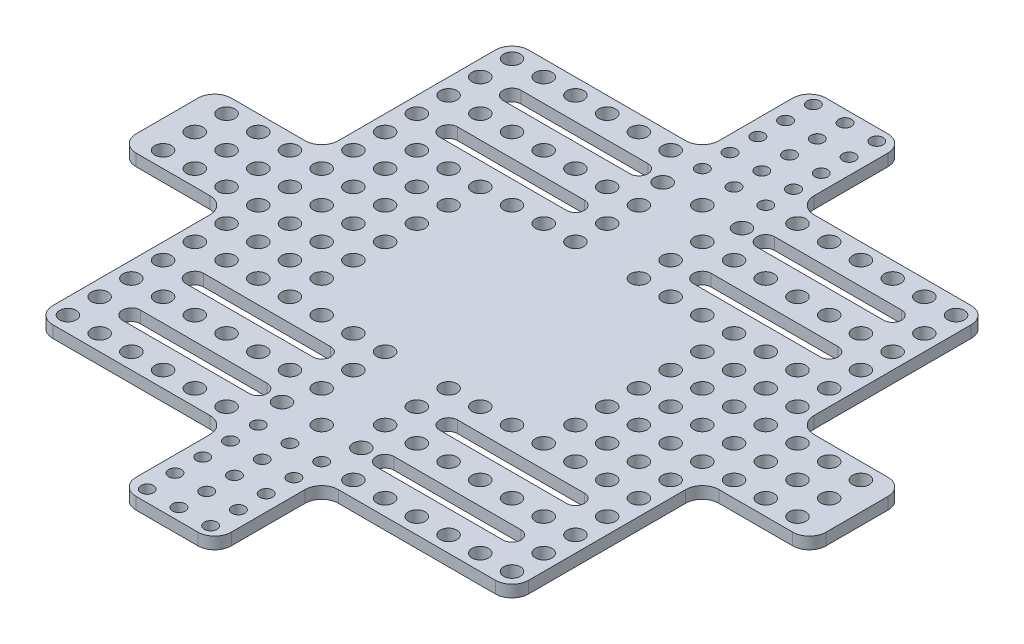
SolidWorks part; units mm, degrees
ref_plane "前视基准面" through (0, 0, 0) normal (0, 0, 1) x (1, 0, 0)
ref_plane "上视基准面" through (0, 0, 0) normal (0, 1, 0) x (1, 0, 0)
ref_plane "右视基准面" through (0, 0, 0) normal (1, 0, 0) x (0, 0, -1)
sketch "草图1" plane through (0, 0, 0) normal (0, 1, 0) x (1, 0, 0)
  line L0 (87, -12) -> (60, -12)
  line L1 (-60, 60) -> (-12, 60)
  line L2 (-60, 60) -> (-60, 12)
  line L3 (-60, -60) -> (-12, -60)
  line L4 (60, 60) -> (60, 12)
  line L5 (-60, 60) -> (60, -60) construction
  line L6 (-60, -60) -> (60, 60) construction
  line L7 (-12, 87) -> (12, 87)
  line L8 (-12, 87) -> (-12, 60)
  line L10 (12, 87) -> (12, 60)
  line L11 (87, 12) -> (60, 12)
  line L12 (87, -12) -> (87, 12)
  line L13 (-87, -12) -> (-60, -12)
  line L14 (-87, 12) -> (-60, 12)
  line L15 (-87, 12) -> (-87, -12)
  line L16 (12, -87) -> (-12, -87)
  line L17 (-12, -87) -> (-12, -60)
  line L18 (12, -87) -> (12, -60)
  line L19 (12, 60) -> (60, 60)
  line L20 (60, -12) -> (60, -60)
  line L21 (-60, -12) -> (-60, -60)
  line L22 (12, -60) -> (60, -60)
  line L23 (-56, 56) -> (-48, 56) construction
  line L24 (0, -20.5615) -> (0, 20.5615) construction
  line L25 (0, 56) -> (0, 63) construction
  line L26 (-56, 16) -> (-48, 16) construction
  line L27 (-56, 16) -> (-56, 8) construction
  line L28 (56, 16) -> (56, 8) construction
  line L29 (56, 16) -> (48, 16) construction
  line L30 (-48, 48) -> (-16, 48) construction
  line L31 (-48, 50.25) -> (-16, 50.25)
  line L32 (-48, 45.75) -> (-16, 45.75)
  line L33 (-56, 40) -> (-48, 40) construction
  line L34 (-48, 32) -> (-16, 32) construction
  line L35 (-48, 34.25) -> (-16, 34.25)
  line L36 (-48, 29.75) -> (-16, 29.75)
  line L37 (-48, 48) -> (-48, 32) construction
  line L38 (48, 32) -> (16, 32) construction
  line L39 (48, 34.25) -> (16, 34.25)
  line L40 (48, 29.75) -> (16, 29.75)
  line L41 (48, 48) -> (16, 48) construction
  line L42 (48, 50.25) -> (16, 50.25)
  line L43 (48, 45.75) -> (16, 45.75)
  line L44 (-55, 0) -> (55, 0) construction
  line L45 (-48, -48) -> (-16, -48) construction
  line L46 (-48, -50.25) -> (-16, -50.25)
  line L47 (-48, -45.75) -> (-16, -45.75)
  line L48 (48, -48) -> (16, -48) construction
  line L49 (48, -50.25) -> (16, -50.25)
  line L50 (48, -45.75) -> (16, -45.75)
  line L51 (-48, -32) -> (-16, -32) construction
  line L52 (-48, -34.25) -> (-16, -34.25)
  line L53 (-48, -29.75) -> (-16, -29.75)
  line L54 (48, -32) -> (16, -32) construction
  line L55 (48, -34.25) -> (16, -34.25)
  line L56 (48, -29.75) -> (16, -29.75)
  line L57 (-56, 8) -> (-64, 8) construction
  line L58 (-8, 40) -> (-8, 32) construction
  circle A0 centre (0, 56) radius 1.6
  circle A1 centre (-56, 56) radius 2.1
  circle A2 centre (-48, 56) radius 2.1
  circle A3 centre (-40, 56) radius 2.1
  circle A4 centre (-32, 56) radius 2.1
  circle A5 centre (-24, 56) radius 2.1
  circle A6 centre (-16, 56) radius 2.1
  circle A7 centre (-8, 56) radius 1.6
  circle A8 centre (8, 56) radius 1.6
  circle A9 centre (0, 63) radius 1.6
  circle A10 centre (-8, 63) radius 1.6
  circle A11 centre (8, 63) radius 1.6
  circle A12 centre (0, 70) radius 1.6
  circle A13 centre (-8, 70) radius 1.6
  circle A14 centre (8, 70) radius 1.6
  circle A15 centre (0, 77) radius 1.6
  circle A16 centre (-8, 77) radius 1.6
  circle A17 centre (8, 77) radius 1.6
  circle A18 centre (0, 84) radius 1.6
  circle A19 centre (-8, 84) radius 1.6
  circle A20 centre (8, 84) radius 1.6
  circle A21 centre (0, 48) radius 2.1
  circle A22 centre (-10, 48) radius 2.1
  circle A23 centre (10, 48) radius 2.1
  circle A24 centre (-56, 16) radius 2.1
  circle A25 centre (-56, 24) radius 2.1
  circle A26 centre (-56, 32) radius 2.1
  circle A27 centre (-56, 40) radius 2.1
  circle A28 centre (-56, 48) radius 2.1
  circle A29 centre (-48, 16) radius 2.1
  circle A30 centre (-40, 16) radius 2.1
  circle A31 centre (-32, 16) radius 2.1
  circle A32 centre (-48, 8) radius 2.1
  circle A33 centre (-40, 8) radius 2.1
  circle A34 centre (-32, 8) radius 2.1
  circle A35 centre (-48, 0) radius 2.1
  circle A36 centre (-40, 0) radius 2.1
  circle A37 centre (-32, 0) radius 2.1
  circle A38 centre (-48, -8) radius 2.1
  circle A39 centre (-40, -8) radius 2.1
  circle A40 centre (-32, -8) radius 2.1
  circle A41 centre (-48, -16) radius 2.1
  circle A42 centre (-40, -16) radius 2.1
  circle A43 centre (-32, -16) radius 2.1
  circle A44 centre (-56, 8) radius 2.1
  circle A45 centre (-56, 0) radius 2.1
  circle A46 centre (-56, -8) radius 2.1
  circle A47 centre (-56, -16) radius 2.1
  circle A48 centre (56, -16) radius 2.1
  circle A49 centre (56, -8) radius 2.1
  circle A50 centre (56, 0) radius 2.1
  circle A51 centre (56, 8) radius 2.1
  circle A52 centre (32, -16) radius 2.1
  circle A53 centre (40, -16) radius 2.1
  circle A54 centre (48, -16) radius 2.1
  circle A55 centre (32, -8) radius 2.1
  circle A56 centre (40, -8) radius 2.1
  circle A57 centre (48, -8) radius 2.1
  circle A58 centre (32, 0) radius 2.1
  circle A59 centre (40, 0) radius 2.1
  circle A60 centre (48, 0) radius 2.1
  circle A61 centre (32, 8) radius 2.1
  circle A62 centre (40, 8) radius 2.1
  circle A63 centre (48, 8) radius 2.1
  circle A64 centre (32, 16) radius 2.1
  circle A65 centre (40, 16) radius 2.1
  circle A66 centre (48, 16) radius 2.1
  circle A67 centre (56, 16) radius 2.1
  arc A68 (-48, 50.25) -> (-48, 45.75) centre (-48, 48) ccw
  arc A69 (-16, 45.75) -> (-16, 50.25) centre (-16, 48) ccw
  circle A70 centre (-48, 40) radius 2.1
  circle A71 centre (-40, 40) radius 2.1
  circle A72 centre (-32, 40) radius 2.1
  circle A73 centre (-24, 40) radius 2.1
  circle A74 centre (-16, 40) radius 2.1
  circle A75 centre (-8, 40) radius 2.1
  circle A76 centre (-16, 24) radius 2.1
  circle A77 centre (-24, 24) radius 2.1
  circle A78 centre (-32, 24) radius 2.1
  circle A79 centre (-48, 24) radius 2.1
  circle A80 centre (-40, 24) radius 2.1
  circle A82 centre (-8, 24) radius 2.1
  arc A83 (-48, 34.25) -> (-48, 29.75) centre (-48, 32) ccw
  arc A84 (-16, 29.75) -> (-16, 34.25) centre (-16, 32) ccw
  circle A85 centre (8, 24) radius 2.1
  circle A86 centre (16, 24) radius 2.1
  circle A87 centre (24, 24) radius 2.1
  circle A88 centre (32, 24) radius 2.1
  circle A89 centre (40, 24) radius 2.1
  circle A90 centre (48, 24) radius 2.1
  circle A91 centre (56, 24) radius 2.1
  circle A92 centre (56, 32) radius 2.1
  arc A93 (48, 34.25) -> (48, 29.75) centre (48, 32) cw
  arc A94 (16, 29.75) -> (16, 34.25) centre (16, 32) cw
  circle A96 centre (8, 40) radius 2.1
  circle A97 centre (16, 40) radius 2.1
  circle A98 centre (24, 40) radius 2.1
  circle A99 centre (32, 40) radius 2.1
  circle A100 centre (40, 40) radius 2.1
  circle A101 centre (48, 40) radius 2.1
  circle A102 centre (56, 40) radius 2.1
  circle A103 centre (56, 48) radius 2.1
  arc A104 (48, 50.25) -> (48, 45.75) centre (48, 48) cw
  arc A105 (16, 45.75) -> (16, 50.25) centre (16, 48) cw
  circle A106 centre (16, 56) radius 2.1
  circle A107 centre (24, 56) radius 2.1
  circle A108 centre (32, 56) radius 2.1
  circle A109 centre (40, 56) radius 2.1
  circle A110 centre (48, 56) radius 2.1
  circle A111 centre (56, 56) radius 2.1
  circle A112 centre (8, -77) radius 1.6
  circle A113 centre (8, -84) radius 1.6
  circle A114 centre (0, -84) radius 1.6
  circle A115 centre (-8, -84) radius 1.6
  circle A116 centre (-8, -77) radius 1.6
  circle A117 centre (0, -77) radius 1.6
  circle A118 centre (8, -70) radius 1.6
  circle A119 centre (0, -70) radius 1.6
  circle A120 centre (-8, -70) radius 1.6
  circle A121 centre (-8, -63) radius 1.6
  circle A122 centre (0, -63) radius 1.6
  circle A123 centre (8, -63) radius 1.6
  circle A124 centre (24, -56) radius 2.1
  circle A125 centre (16, -56) radius 2.1
  circle A126 centre (8, -56) radius 1.6
  circle A127 centre (0, -56) radius 1.6
  circle A128 centre (-8, -56) radius 1.6
  circle A129 centre (-16, -56) radius 2.1
  circle A130 centre (-24, -56) radius 2.1
  circle A131 centre (-32, -56) radius 2.1
  circle A132 centre (-40, -56) radius 2.1
  circle A133 centre (-48, -56) radius 2.1
  circle A134 centre (-56, -56) radius 2.1
  circle A135 centre (-56, -48) radius 2.1
  circle A136 centre (10, -48) radius 2.1
  circle A137 centre (0, -48) radius 2.1
  circle A138 centre (-10, -48) radius 2.1
  arc A139 (-48, -50.25) -> (-48, -45.75) centre (-48, -48) cw
  arc A140 (-16, -45.75) -> (-16, -50.25) centre (-16, -48) cw
  arc A141 (48, -50.25) -> (48, -45.75) centre (48, -48) ccw
  arc A142 (16, -45.75) -> (16, -50.25) centre (16, -48) ccw
  circle A143 centre (32, -56) radius 2.1
  circle A144 centre (40, -56) radius 2.1
  circle A145 centre (48, -56) radius 2.1
  circle A146 centre (56, -56) radius 2.1
  circle A147 centre (56, -48) radius 2.1
  circle A148 centre (56, -40) radius 2.1
  circle A149 centre (48, -40) radius 2.1
  circle A150 centre (40, -40) radius 2.1
  circle A151 centre (32, -40) radius 2.1
  circle A152 centre (24, -40) radius 2.1
  circle A153 centre (16, -40) radius 2.1
  circle A154 centre (8, -40) radius 2.1
  circle A155 centre (-8, -40) radius 2.1
  circle A156 centre (-16, -40) radius 2.1
  circle A157 centre (-24, -40) radius 2.1
  circle A158 centre (-32, -40) radius 2.1
  circle A159 centre (-40, -40) radius 2.1
  circle A160 centre (-48, -40) radius 2.1
  circle A161 centre (-56, -40) radius 2.1
  circle A162 centre (-56, -32) radius 2.1
  arc A163 (-48, -34.25) -> (-48, -29.75) centre (-48, -32) cw
  arc A164 (-16, -29.75) -> (-16, -34.25) centre (-16, -32) cw
  arc A167 (48, -34.25) -> (48, -29.75) centre (48, -32) ccw
  arc A168 (16, -29.75) -> (16, -34.25) centre (16, -32) ccw
  circle A169 centre (56, -32) radius 2.1
  circle A170 centre (56, -24) radius 2.1
  circle A171 centre (48, -24) radius 2.1
  circle A172 centre (40, -24) radius 2.1
  circle A173 centre (32, -24) radius 2.1
  circle A174 centre (24, -24) radius 2.1
  circle A175 centre (16, -24) radius 2.1
  circle A176 centre (8, -24) radius 2.1
  circle A177 centre (-8, -24) radius 2.1
  circle A178 centre (-16, -24) radius 2.1
  circle A179 centre (-24, -24) radius 2.1
  circle A180 centre (-32, -24) radius 2.1
  circle A181 centre (-40, -24) radius 2.1
  circle A182 centre (-48, -24) radius 2.1
  circle A183 centre (-56, -24) radius 2.1
  circle A184 centre (-64, 8) radius 2.1
  circle A185 centre (-64, 0) radius 2.1
  circle A186 centre (-64, -8) radius 2.1
  circle A187 centre (-72, 8) radius 2.1
  circle A188 centre (-72, 0) radius 2.1
  circle A189 centre (-72, -8) radius 2.1
  circle A190 centre (-80, 8) radius 2.1
  circle A191 centre (-80, 0) radius 2.1
  circle A192 centre (-80, -8) radius 2.1
  circle A193 centre (80, -8) radius 2.1
  circle A194 centre (80, 0) radius 2.1
  circle A195 centre (80, 8) radius 2.1
  circle A196 centre (72, -8) radius 2.1
  circle A197 centre (72, 0) radius 2.1
  circle A198 centre (72, 8) radius 2.1
  circle A199 centre (64, -8) radius 2.1
  circle A200 centre (64, 0) radius 2.1
  circle A201 centre (64, 8) radius 2.1
  circle A202 centre (-10, 32) radius 2.1 [skipped]
  circle A203 centre (-8, 32) radius 2.1
  circle A204 centre (8, 32) radius 2.1
  circle A205 centre (8, -32) radius 2.1
  circle A206 centre (-8, -32) radius 2.1
  point P0 (0, 0)
  point P10 (0, 87)
  point P170 (-32, 48)
  point P177 (-32, 45.75)
  point P196 (-32, 32)
  point P231 (32, 32)
  point P256 (32, 48)
  point P331 (-32, -48)
  point P338 (32, -48)
  point P385 (-32, -32)
  point P396 (32, -32)
  dimension "D1" = 3.2
  dimension "D5" = 4.2
  dimension "D10" = 3.2
  dimension "D14" = 4.2
  dimension "D15" = 8
  dimension "D16" = 4.2
  dimension "D17" = 4.2
  dimension "D31" = 10
  dimension "D2" = 120
  dimension "D3" = 27
  dimension "D4" = 24
  dimension "D6" = 4
  dimension "D7" = 4
  dimension "D9" = 8
  dimension "D11" = 8
  dimension "D13" = 7
  dimension "D19" = 8
  dimension "D21" = 8
  dimension "D22" = 90
  dimension "D23" = 4.5
  dimension "D25" = 8
  dimension "D27" = 16
  dimension "D29" = 8
  dimension "D30" = 10
  dimension "D33" = 8
  dimension "D8" = 6
  dimension "D12" = 5
  dimension "D18" = 4
  dimension "D20" = 5
  dimension "D24" = 7
  dimension "D26" = 2
  dimension "D28" = 4
  dimension "D32" = 2
extrude "凸台-拉伸1" add sketch "草图1" along normal blind 3
fillet "圆角1" radius 4.2 20 edges at (-12, 1.5, 87) (12, 1.5, 87) (60, 1.5, 12) (87, 1.5, 12) (87, 1.5, -12) (60, 1.5, -12) (60, 1.5, -60) (12, 1.5, -60) (12, 1.5, -87) (-12, 1.5, -87) (-12, 1.5, -60) (-60, 1.5, -60) (-60, 1.5, -12) (-87, 1.5, -12) (-87, 1.5, 12) (-60, 1.5, 12) (-60, 1.5, 60) (-12, 1.5, 60) (12, 1.5, 60) (60, 1.5, 60)
